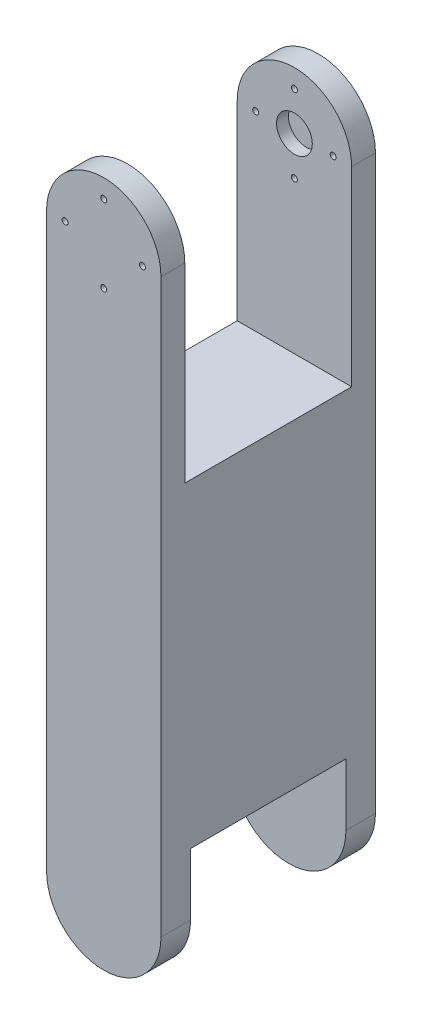
SolidWorks part; units mm, degrees
ref_plane "Front Plane" through (0, 0, 0) normal (0, 0, 1) x (1, 0, 0)
ref_plane "Top Plane" through (0, 0, 0) normal (0, 1, 0) x (1, 0, 0)
ref_plane "Right Plane" through (0, 0, 0) normal (1, 0, 0) x (0, 0, -1)
sketch "Sketch1" plane through (0, 0, 0) normal (0, 0, 1) x (1, 0, 0)
  line L0 (-15.24, 76.2) -> (-15.24, -76.2)
  line L1 (15.24, 76.2) -> (15.24, -76.2)
  line L2 (0, 91.44) -> (0, -91.44) construction
  arc A0 (-15.24, 76.2) -> (15.24, 76.2) centre (0, 76.2) cw
  arc A1 (-15.24, -76.2) -> (15.24, -76.2) centre (0, -76.2) ccw
  point P8 (0, 0)
  dimension "D1" = 30.48
  dimension "D2" = 152.4
extrude "Boss-Extrude1" add sketch "Sketch1" along normal blind 57.15
sketch "Sketch2" plane through (15.24, 0, 0) normal (1, 0, 0) x (0, 0, -1)
  line L0 (0, 91.44) -> (-57.15, 91.44) construction
  line L1 (-50.8, 91.44) -> (-6.35, 91.44)
  line L2 (-50.8, 91.44) -> (-50.8, 25.4)
  line L3 (-50.8, 25.4) -> (-6.35, 25.4)
  line L4 (-6.35, 91.44) -> (-6.35, 25.4)
  line L5 (-57.15, 91.44) -> (-50.8, 91.44) construction
  line L6 (-6.35, 91.44) -> (0, 91.44) construction
  dimension "D1" = 6.35
  dimension "D2" = 66.04
extrude "Cut-Extrude1" cut sketch "Sketch2" against normal blind 57.15
sketch "Sketch5" plane through (0, 0, 0) normal (0, 0, -1) x (-1, 0, 0)
  line L0 (-12.7, 76.2) -> (-15.24, 76.2) construction
  line L1 (-15.24, -76.2) -> (-15.24, 76.2) construction
  line L2 (0, 88.9) -> (0, 91.44) construction
  circle A0 centre (0, 76.2) radius 12.7
  arc A1 (15.24, 76.2) -> (-15.24, 76.2) centre (0, 76.2) ccw construction
  dimension "D1" = 25.4
sketch "Sketch6" plane through (0, 0, 6.35) normal (0, 0, 1) x (1, 0, 0)
  circle A0 centre (0, 76.2) radius 4.7625
  dimension "D1" = 9.525
extrude "Cut-Extrude3" cut sketch "Sketch6" against normal blind 3.175
ref_plane "Plane2" through (0, 0, 28.575) normal (0, 0, 1) x (1, 0, 0)
sketch "Sketch7" plane through (0, 0, 0) normal (0, 0, -1) x (-1, 0, 0)
  circle A0 centre (0, 76.2) radius 10.3188
  circle A1 centre (0, 76.2) radius 12.7 construction
  dimension "D1" = 2.3812
sketch "Sketch8" plane through (0, 0, 0) normal (0, 0, -1) x (-1, 0, 0)
  circle A0 centre (0, 65.8812) radius 0.7937
  circle A1 centre (0, 76.2) radius 10.3188 construction
  circle A2 centre (-10.3188, 76.2) radius 0.7937
  circle A3 centre (0, 86.5187) radius 0.7937
  circle A4 centre (10.3188, 76.2) radius 0.7938
  point P13 (0, 76.2)
  dimension "D1" = 1.5875
  dimension "D2" = 4
extrude "Cut-Extrude4" cut sketch "Sketch8" against normal through all
sketch "Sketch9" plane through (15.24, 0, 0) normal (1, 0, 0) x (0, 0, -1)
  line L0 (-57.15, -91.44) -> (0, -91.44) construction
  line L1 (-49.276, -91.44) -> (-7.874, -91.44)
  line L2 (-49.276, -91.44) -> (-49.276, -59.69)
  line L3 (-49.276, -59.69) -> (-7.874, -59.69)
  line L4 (-7.874, -91.44) -> (-7.874, -59.69)
  line L5 (-57.15, -71.0088) -> (0, -71.0088) construction
  line L6 (-57.15, -76.2) -> (-57.15, 76.2) construction
  line L7 (0, -76.2) -> (0, 76.2) construction
  point P12 (-28.575, -71.0088)
  point P13 (-28.575, -59.69)
  dimension "D1" = 41.402
  dimension "D2" = 31.75
extrude "Cut-Extrude5" cut sketch "Sketch9" against normal through all
